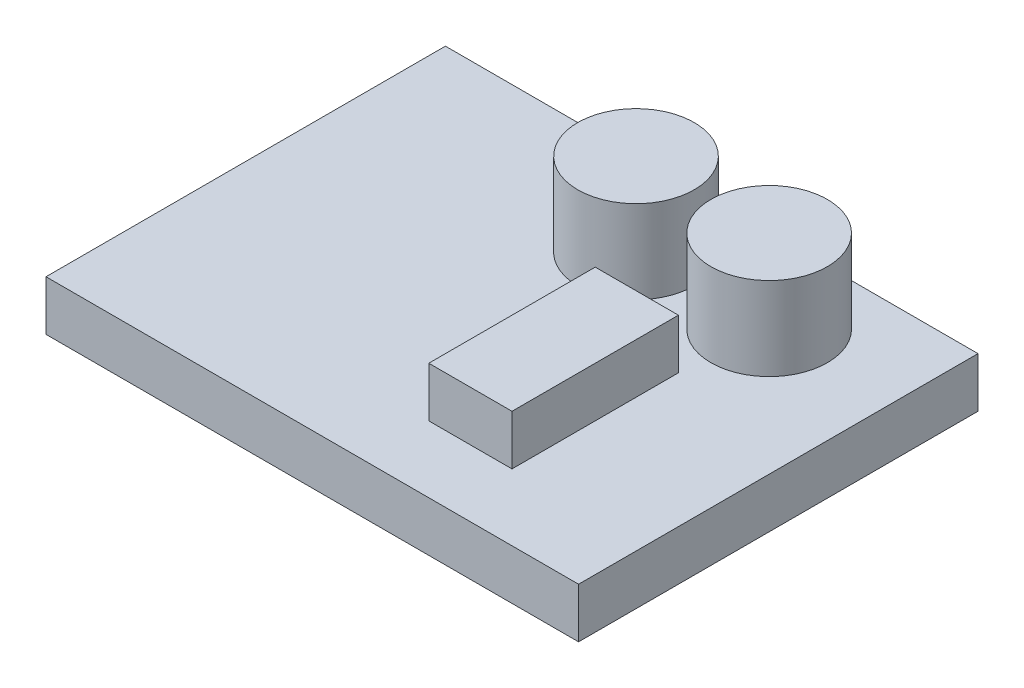
SolidWorks part; units mm, degrees
ref_plane "Front Plane" through (0, 0, 0) normal (0, 0, 1) x (1, 0, 0)
ref_plane "Top Plane" through (0, 0, 0) normal (0, 1, 0) x (1, 0, 0)
ref_plane "Right Plane" through (0, 0, 0) normal (1, 0, 0) x (0, 0, -1)
sketch "Sketch1" plane through (0, 0, 0) normal (0, 1, 0) x (1, 0, 0)
  line L1 (-15.3725, 11.5294) -> (16.6275, 11.5294)
  line L2 (-15.3725, 11.5294) -> (-15.3725, -12.4706)
  line L3 (-15.3725, -12.4706) -> (16.6275, -12.4706)
  line L4 (16.6275, 11.5294) -> (16.6275, -12.4706)
  dimension "D1" = 32
  dimension "D2" = 24
extrude "Boss-Extrude1" add sketch "Sketch1" along normal blind 3
sketch "Sketch2" plane through (0, 3, 0) normal (0, 1, 0) x (1, 0, 0)
  line L0 (16.6275, 11.5294) -> (-15.3725, 11.5294) construction
  circle A0 centre (1.0782, 6.5294) radius 3.5
  circle A1 centre (9.0782, 6.5294) radius 3.5
  dimension "D1" = 7
  dimension "D2" = 7
  dimension "D4" = 5
  dimension "D3" = 8
extrude "Boss-Extrude2" add sketch "Sketch2" along normal blind 5
sketch "Sketch3" plane through (0, 3, 0) normal (0, 1, 0) x (1, 0, 0)
  line L0 (-15.3725, -12.4706) -> (16.6275, -12.4706) construction
  line L1 (3.6275, 1.5294) -> (8.6275, 1.5294)
  line L2 (3.6275, 1.5294) -> (3.6275, -8.4706)
  line L3 (3.6275, -8.4706) -> (8.6275, -8.4706)
  line L4 (8.6275, 1.5294) -> (8.6275, -8.4706)
  line L5 (16.6275, -12.4706) -> (16.6275, 11.5294) construction
  dimension "D1" = 5
  dimension "D2" = 10
  dimension "D3" = 4
  dimension "D4" = 8
extrude "Boss-Extrude3" add sketch "Sketch3" along normal blind 3
